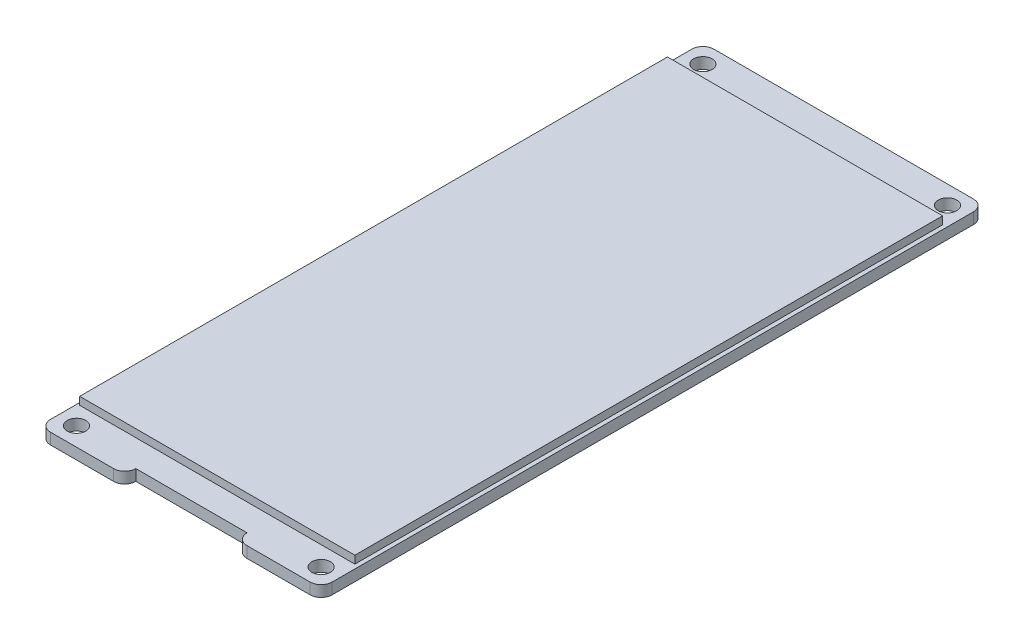
SolidWorks part; units mm, degrees
ref_plane "Front Plane" through (0, 0, 0) normal (0, 0, 1) x (1, 0, 0)
ref_plane "Top Plane" through (0, 0, 0) normal (0, 1, 0) x (1, 0, 0)
ref_plane "Right Plane" through (0, 0, 0) normal (1, 0, 0) x (0, 0, -1)
sketch "Sketch1" plane through (0, 0, 0) normal (0, 1, 0) x (1, 0, 0)
  line L1 (1.5, 0) -> (10, 0)
  line L2 (0, 1.5) -> (0, 88)
  line L3 (1.5, 89.5) -> (36.5, 89.5)
  line L4 (38, 1.5) -> (38, 88)
  line L5 (11.5, 1.5) -> (26.5, 1.5)
  line L7 (28, 0) -> (36.5, 0)
  arc A0 (36.5, 0) -> (38, 1.5) centre (36.5, 1.5) ccw
  arc A1 (1.5, 0) -> (0, 1.5) centre (1.5, 1.5) cw
  arc A2 (36.5, 89.5) -> (38, 88) centre (36.5, 88) cw
  arc A3 (0, 88) -> (1.5, 89.5) centre (1.5, 88) cw
  arc A4 (26.5, 1.5) -> (28, 0) centre (28, 1.5) ccw
  arc A5 (11.5, 1.5) -> (10, 0) centre (10, 1.5) cw
  circle A6 centre (2.5, 2.5) radius 1.25
  circle A7 centre (35.5, 2.5) radius 1.25
  circle A8 centre (35.5, 87) radius 1.25
  circle A9 centre (2.5, 87) radius 1.25
  point P7 (38, 0)
  point P10 (0, 0)
  point P13 (38, 89.5)
  point P16 (0, 89.5)
  point P25 (26.5, 0)
  dimension "D3" = 1.5
  dimension "D4" = 1.5
  dimension "D5" = 1.5
  dimension "D6" = 1.5
  dimension "D9" = 1.5
  dimension "D10" = 1.5
  dimension "D13" = 2.5
  dimension "D16" = 2.5
  dimension "D21" = 2.5
  dimension "D22" = 2.5
  dimension "D1" = 38
  dimension "D2" = 89.5
  dimension "D7" = 11.5
  dimension "D8" = 11.5
  dimension "D11" = 2.5
  dimension "D12" = 2.5
  dimension "D14" = 2.5
  dimension "D15" = 2.5
  dimension "D17" = 2.5
  dimension "D18" = 2.5
  dimension "D19" = 2.5
  dimension "D20" = 2.5
extrude "Boss-Extrude1" add sketch "Sketch1" along normal blind 1.5
sketch "Sketch2" plane through (0, 1.5, 0) normal (0, 1, 0) x (1, 0, 0)
  line L1 (0.3217, 5.1079) -> (37.4403, 5.1079)
  line L2 (0.3217, 5.1079) -> (0.3217, 84.4033)
  line L3 (0.3217, 84.4033) -> (37.4403, 84.4033)
  line L4 (37.4403, 5.1079) -> (37.4403, 84.4033)
extrude "Boss-Extrude2" add sketch "Sketch2" along normal blind 1.05
sketch "Sketch3" plane through (0, 0, 0) normal (0, -1, 0) x (1, 0, 0)
  line L0 (23.5029, -20.6675) -> (23.5029, -18.6595)
  line L1 (13.8398, -38.8426) -> (15.0426, -38.8426)
  line L2 (13.8398, -38.8426) -> (13.8398, -41.6281)
  line L3 (13.8398, -41.6281) -> (15.0426, -41.6281)
  line L4 (15.0426, -38.8426) -> (15.0426, -41.6281)
  line L5 (16.7134, -24.2664) -> (18.2261, -24.2664)
  line L6 (16.7134, -24.2664) -> (16.7134, -28.811)
  line L7 (16.7134, -28.811) -> (18.2261, -28.811)
  line L8 (18.2261, -24.2664) -> (18.2261, -28.811)
  line L9 (20.1328, -28.811) -> (21.4951, -28.811)
  line L10 (20.1328, -28.811) -> (20.1328, -24.2664)
  line L11 (20.1328, -24.2664) -> (21.4951, -24.2664)
  line L12 (21.4951, -28.811) -> (21.4951, -24.2664)
  line L13 (23.7042, -24.2664) -> (24.8839, -24.2664)
  line L14 (23.7042, -24.2664) -> (23.7042, -28.811)
  line L15 (23.7042, -28.811) -> (24.8839, -28.811)
  line L16 (24.8839, -24.2664) -> (24.8839, -28.811)
  line L17 (25.3529, -20.6675) -> (24.6465, -20.6675)
  line L18 (25.3529, -20.6675) -> (25.3529, -18.6595)
  line L19 (25.3529, -18.6595) -> (24.6465, -18.6595)
  line L20 (24.6465, -20.6675) -> (24.6465, -18.6595)
  line L21 (23.5029, -20.6675) -> (22.7965, -20.6675)
  line L22 (22.7965, -20.6675) -> (22.7965, -18.6595)
  line L23 (23.5029, -18.6595) -> (22.7965, -18.6595)
  line L24 (21.6529, -20.6675) -> (21.6529, -18.6595)
  line L25 (21.6529, -20.6675) -> (20.9465, -20.6675)
  line L26 (20.9465, -20.6675) -> (20.9465, -18.6595)
  line L27 (21.6529, -18.6595) -> (20.9465, -18.6595)
  line L28 (19.8029, -20.6675) -> (19.8029, -18.6595)
  line L29 (19.8029, -20.6675) -> (19.0965, -20.6675)
  line L30 (19.0965, -20.6675) -> (19.0965, -18.6595)
  line L31 (19.8029, -18.6595) -> (19.0965, -18.6595)
  line L32 (17.9529, -20.6675) -> (17.9529, -18.6595)
  line L33 (17.9529, -20.6675) -> (17.2465, -20.6675)
  line L34 (17.2465, -20.6675) -> (17.2465, -18.6595)
  line L35 (17.9529, -18.6595) -> (17.2465, -18.6595)
  line L36 (16.1029, -20.6675) -> (16.1029, -18.6595)
  line L37 (16.1029, -20.6675) -> (15.3965, -20.6675)
  line L38 (15.3965, -20.6675) -> (15.3965, -18.6595)
  line L39 (16.1029, -18.6595) -> (15.3965, -18.6595)
  line L41 (11.9603, -20.1559) -> (13.8398, -20.1559)
  line L42 (11.9603, -20.1559) -> (11.9603, -18.9977)
  line L43 (11.9603, -18.9977) -> (13.8398, -18.9977)
  line L44 (13.8398, -20.1559) -> (13.8398, -18.9977)
  line L48 (23.5029, -16.0675) -> (23.5029, -14.0595)
  line L49 (23.5029, -16.0675) -> (22.7965, -16.0675)
  line L50 (22.7965, -16.0675) -> (22.7965, -14.0595)
  line L51 (23.5029, -14.0595) -> (22.7965, -14.0595)
  line L52 (21.6529, -16.0675) -> (21.6529, -14.0595)
  line L53 (21.6529, -16.0675) -> (20.9465, -16.0675)
  line L54 (20.9465, -16.0675) -> (20.9465, -14.0595)
  line L55 (21.6529, -14.0595) -> (20.9465, -14.0595)
  line L56 (19.8029, -16.0675) -> (19.8029, -14.0595)
  line L57 (19.8029, -16.0675) -> (19.0965, -16.0675)
  line L58 (19.0965, -16.0675) -> (19.0965, -14.0595)
  line L59 (19.8029, -14.0595) -> (19.0965, -14.0595)
  line L60 (17.9529, -16.0675) -> (17.9529, -14.0595)
  line L61 (17.9529, -16.0675) -> (17.2465, -16.0675)
  line L62 (17.2465, -16.0675) -> (17.2465, -14.0595)
  line L63 (17.9529, -14.0595) -> (17.2465, -14.0595)
  line L64 (16.1029, -16.0675) -> (16.1029, -14.0595)
  line L65 (16.1029, -16.0675) -> (15.3965, -16.0675)
  line L66 (15.3965, -16.0675) -> (15.3965, -14.0595)
  line L67 (16.1029, -14.0595) -> (15.3965, -14.0595)
  line L68 (14.2529, -16.0675) -> (14.2529, -14.0595)
  line L69 (14.2529, -16.0675) -> (13.5465, -16.0675)
  line L70 (13.5465, -16.0675) -> (13.5465, -14.0595)
  line L71 (14.2529, -14.0595) -> (13.5465, -14.0595)
  line L72 (12.4029, -16.0675) -> (12.4029, -14.0595)
  line L73 (12.4029, -16.0675) -> (11.6965, -16.0675)
  line L74 (11.6965, -16.0675) -> (11.6965, -14.0595)
  line L75 (12.4029, -14.0595) -> (11.6965, -14.0595)
  line L76 (25.3529, -16.0675) -> (25.3529, -14.0595)
  line L77 (25.3529, -16.0675) -> (24.6465, -16.0675)
  line L78 (24.6465, -16.0675) -> (24.6465, -14.0595)
  line L79 (25.3529, -14.0595) -> (24.6465, -14.0595)
  line L80 (14.2529, -20.6675) -> (14.2529, -18.6595) [skipped]
  line L81 (13.5465, -20.6675) -> (13.5465, -18.6595) [skipped]
  line L82 (12.4029, -20.6675) -> (12.4029, -18.6595) [skipped]
  line L83 (11.6965, -20.6675) -> (11.6965, -18.6595) [skipped]
  line L84 (12.4029, -20.6675) -> (11.6965, -20.6675) [skipped]
  line L85 (14.2529, -20.6675) -> (13.5465, -20.6675) [skipped]
  line L86 (12.4029, -18.6595) -> (11.6965, -18.6595) [skipped]
  line L87 (14.2529, -18.6595) -> (13.5465, -18.6595) [skipped]
  circle A0 centre (13.1443, -26.5393) radius 1.481
  dimension "D1" = 8
  dimension "D2" = 2
extrude "Boss-Extrude3" add sketch "Sketch3" along normal blind 1
